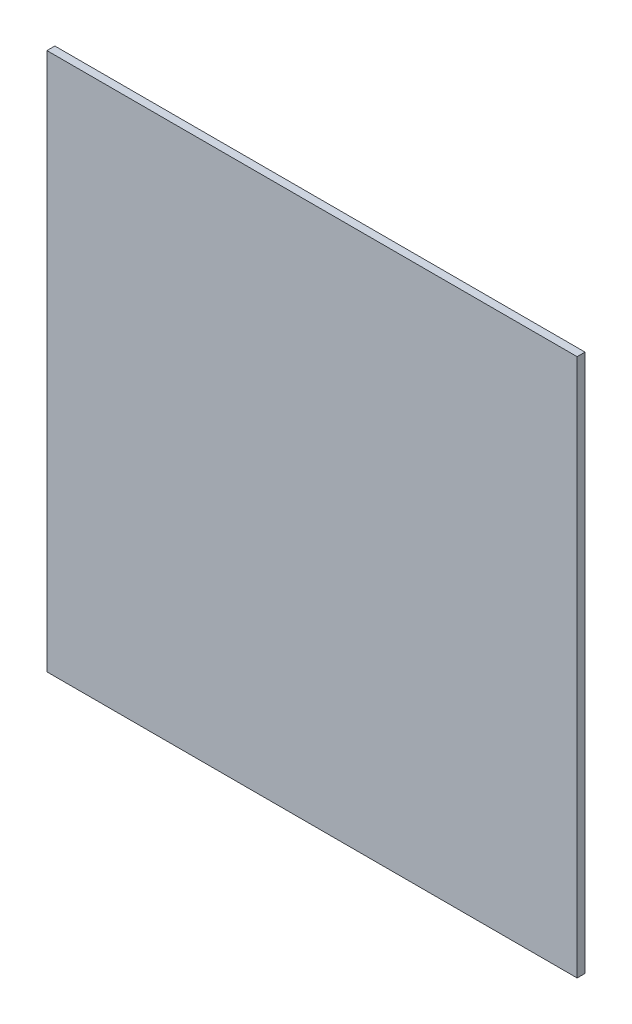
SolidWorks part; units mm, degrees
ref_plane "Front Plane" through (0, 0, 0) normal (0, 0, 1) x (1, 0, 0)
ref_plane "Top Plane" through (0, 0, 0) normal (0, 1, 0) x (1, 0, 0)
ref_plane "Right Plane" through (0, 0, 0) normal (1, 0, 0) x (0, 0, -1)
sketch "Sketch1" plane through (0, 0, 0) normal (0, 0, 1) x (1, 0, 0)
  line L1 (0, 0) -> (670, 0)
  line L2 (0, 0) -> (0, 680)
  line L3 (0, 680) -> (670, 680)
  line L4 (670, 0) -> (670, 680)
  dimension "D1" = 680
  dimension "D2" = 670
extrude "Extrude1" add sketch "Sketch1" along normal blind 10
